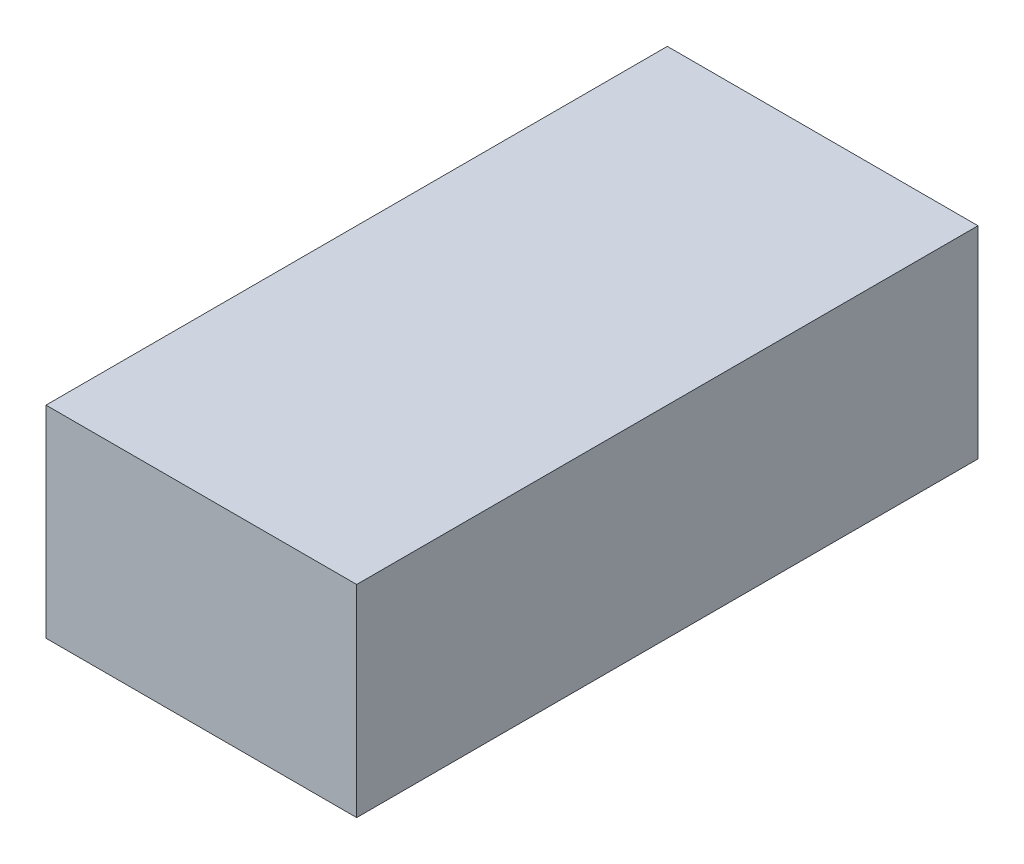
SolidWorks part; units mm, degrees
ref_plane "Front Plane" through (0, 0, 0) normal (0, 0, 1) x (1, 0, 0)
ref_plane "Top Plane" through (0, 0, 0) normal (0, 1, 0) x (1, 0, 0)
ref_plane "Right Plane" through (0, 0, 0) normal (1, 0, 0) x (0, 0, -1)
sketch "Sketch1" plane through (0, 0, 0) normal (1, 0, 0) x (0, 0, -1)
  line L1 (-10, -3.25) -> (10, -3.25)
  line L2 (-10, -3.25) -> (-10, 3.25)
  line L3 (-10, 3.25) -> (10, 3.25)
  line L4 (10, -3.25) -> (10, 3.25)
  line L5 (-10, -3.25) -> (10, 3.25) construction
  line L6 (-10, 3.25) -> (10, -3.25) construction
  point P0 (0, 0)
  dimension "D1" = 6.5
  dimension "D2" = 20
extrude "Boss-Extrude1" add sketch "Sketch1" along normal blind 10
